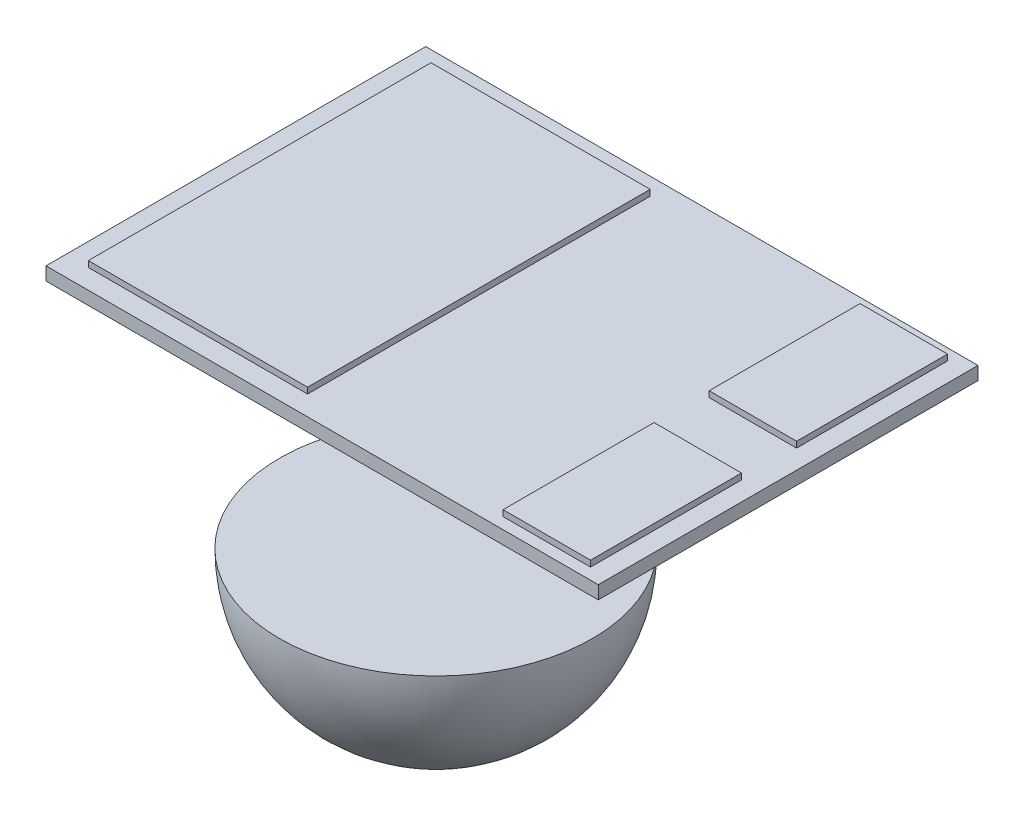
SolidWorks part; units mm, degrees
material "C-Glass Fiber"
ref_plane "Front Plane" through (0, 0, 0) normal (0, 0, 1) x (1, 0, 0)
ref_plane "Plane 1" through (0, 0, 0) normal (0, 1, 0) x (1, 0, 0)
ref_plane "Right Plane" through (0, 0, 0) normal (1, 0, 0) x (0, 0, -1)
sketch "Sketch1" plane through (0, 0, 0) normal (0, 1, 0) x (1, 0, 0)
  line L1 (-1.7924, 1.585) -> (2.8176, 1.585)
  line L2 (-1.7924, 1.585) -> (-1.7924, -1.585)
  line L3 (-1.7924, -1.585) -> (2.8176, -1.585)
  line L4 (2.8176, 1.585) -> (2.8176, -1.585)
  dimension "D1" = 4.61
  dimension "D2" = 3.17
  dimension "D3" = 1.585
extrude "Boss-Extrude1" add sketch "Sketch1" along normal blind 0.11
sketch "Sketch3" plane through (0, 0, 0) normal (0, 1, 0) x (1, 0, 0)
  line L0 (-1.7924, -1.585) -> (2.8176, -1.585) construction
  line L1 (-1.6037, 1.44) -> (0.2263, 1.44)
  line L2 (-1.6037, 1.44) -> (-1.6037, -1.42)
  line L3 (-1.6037, -1.42) -> (0.2263, -1.42)
  line L4 (0.2263, 1.44) -> (0.2263, -1.42)
  dimension "D1" = 2.86
  dimension "D2" = 1.83
  dimension "D3" = 0.165
extrude "Boss-Extrude2" add sketch "Sketch3" along normal blind 0.16
sketch "Sketch4" plane through (0, 0, 0) normal (0, 1, 0) x (1, 0, 0)
  line L0 (-1.7924, -1.585) -> (2.8176, -1.585) construction
  line L1 (1.9281, 1.49) -> (2.6581, 1.49)
  line L2 (1.9281, 1.49) -> (1.9281, 0.23)
  line L3 (1.9281, 0.23) -> (2.6581, 0.23)
  line L4 (2.6581, 1.49) -> (2.6581, 0.23)
  line L5 (1.9281, -0.23) -> (2.6581, -0.23)
  line L6 (1.9281, -0.23) -> (1.9281, -1.49)
  line L7 (1.9281, -1.49) -> (2.6581, -1.49)
  line L8 (2.6581, -0.23) -> (2.6581, -1.49)
  dimension "D1" = 1.26
  dimension "D2" = 1.26
  dimension "D3" = 0.46
  dimension "D4" = 0.095
  dimension "D5" = 0.73
  dimension "D6" = 0.73
extrude "Boss-Extrude3" add sketch "Sketch4" along normal blind 0.16
ref_plane "Plane1" through (0, -1.89, 0) normal (0, -1, 0) x (-1, 0, 0)
sketch "Sketch6" plane through (0, -1.89, 0) normal (0, -1, 0) x (-1, 0, 0)
  line L0 (0.1224, 1.305) -> (0.1224, -1.305)
  arc A0 (0.1224, 1.305) -> (0.1224, -1.305) centre (0.1224, 0) cw
  point P5 (0, 0)
  point P6 (0, 0)
  point P8 (0, 0)
revolve "Revolve3" add sketch "Sketch6" angle 180 about L0
